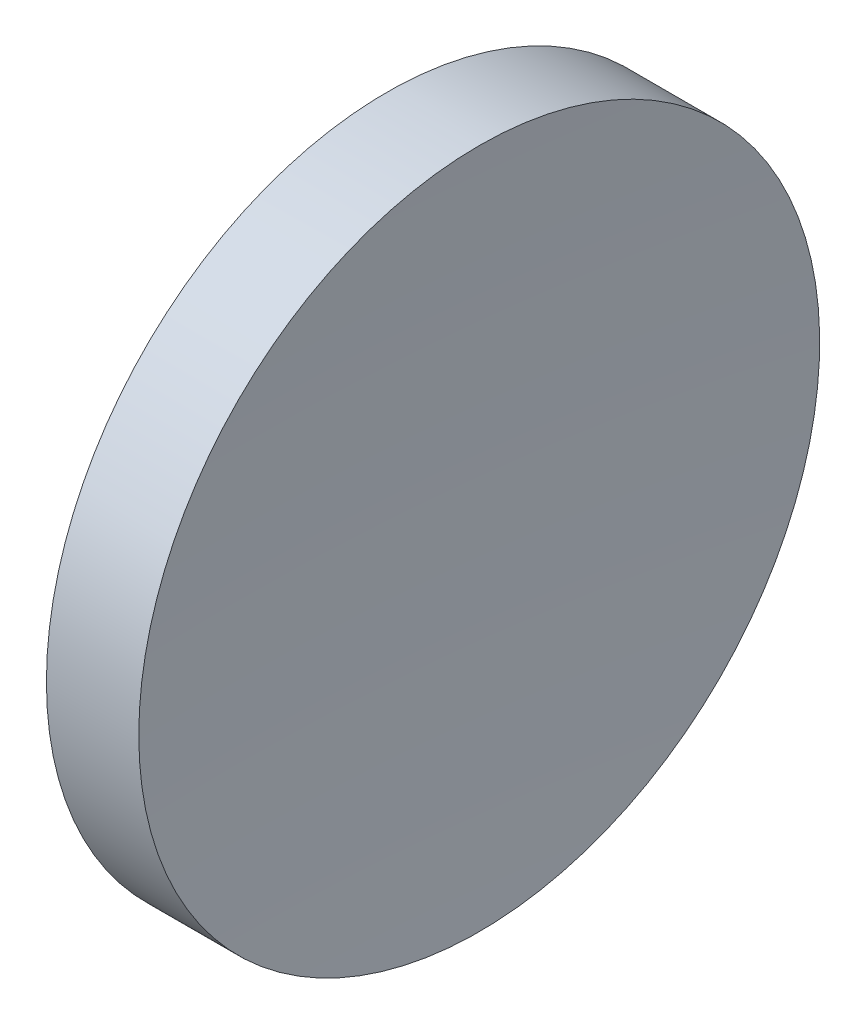
SolidWorks part; units mm, degrees
ref_plane "前视基准面" through (0, 0, 0) normal (0, 0, 1) x (1, 0, 0)
ref_plane "上视基准面" through (0, 0, 0) normal (0, 1, 0) x (1, 0, 0)
ref_plane "右视基准面" through (0, 0, 0) normal (1, 0, 0) x (0, 0, -1)
sketch "草图1" plane through (0, 0, 0) normal (0, 0, 1) x (1, 0, 0)
  line L0 (217.9703, 138.756) -> (265.5527, 138.756) construction
  line L1 (230.1996, 138.756) -> (230.1996, 176.256)
  line L2 (230.1996, 176.256) -> (240.3726, 176.256)
  line L3 (239.1996, 138.756) -> (230.1996, 138.756)
  arc A0 (240.3726, 176.256) -> (239.1996, 138.756) centre (839.1996, 138.756) ccw
revolve "旋转1" add sketch "草图1" angle 360 about L0
